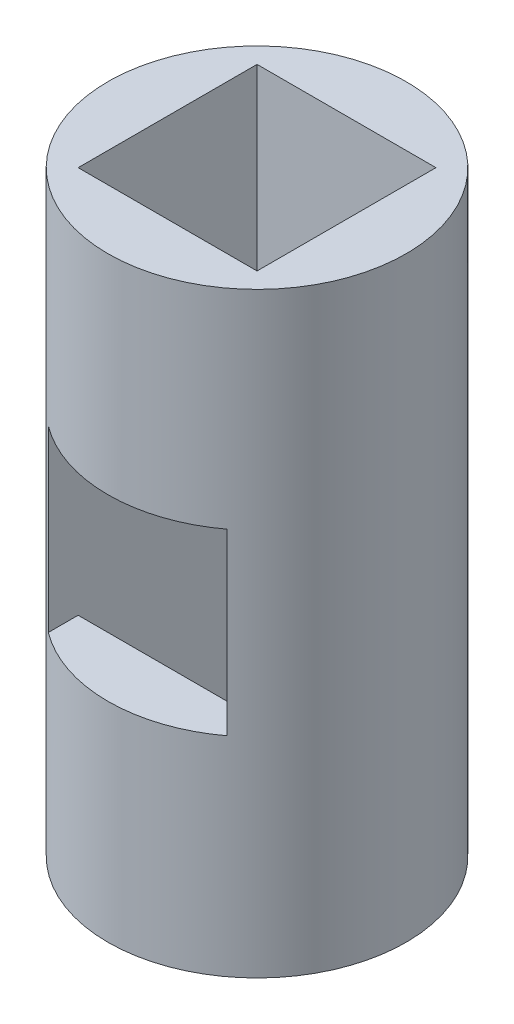
SolidWorks part; units mm, degrees
ref_plane "Front Plane" through (0, 0, 0) normal (0, 0, 1) x (1, 0, 0)
ref_plane "Top Plane" through (0, 0, 0) normal (0, 1, 0) x (1, 0, 0)
ref_plane "Right Plane" through (0, 0, 0) normal (1, 0, 0) x (0, 0, -1)
sketch "Sketch1" plane through (0, 0, 0) normal (0, 1, 0) x (1, 0, 0)
  circle A0 centre (0, 0) radius 25
  dimension "D1" = 50
extrude "Boss-Extrude1" add sketch "Sketch1" along normal blind 100
sketch3d "3DSketch4"
  line L1 (-15, 0, -15) -> (15, 0, -15)
  line L2 (-15, 0, -15) -> (-15, 0, 15)
  line L3 (-15, 0, 15) -> (15, 0, 15)
  line L4 (15, 0, -15) -> (15, 0, 15)
  line L5 (-15, 0, -15) -> (15, 0, 15) construction
  line L6 (-15, 0, 15) -> (15, 0, -15) construction
  point P0 (0, 0, 0)
  dimension "D1" = 30
  dimension "D2" = 30
extrude "Cut-Extrude1" cut sketch "3DSketch4" along a picked direction on the side of the normal up to next (100 mm away)
sketch "Sketch3" plane through (0, 0, -15) normal (0, 0, 1) x (1, 0, 0)
  line L0 (0, 0) -> (0, 100) construction
  line L1 (-15, 100) -> (15, 100) construction
  line L3 (-15, 65) -> (15, 65)
  line L4 (-15, 65) -> (-15, 35)
  line L5 (-15, 35) -> (15, 35)
  line L6 (15, 65) -> (15, 35)
  line L7 (-15, 65) -> (15, 35) construction
  line L8 (-15, 35) -> (15, 65) construction
  point P5 (0, 50)
  dimension "D1" = 30
  dimension "D2" = 30
extrude "Cut-Extrude2" cut sketch "Sketch3" against normal up to next
sketch "Sketch4" plane through (0, 0, 15) normal (0, 0, -1) x (-1, 0, 0)
  line L1 (-15, 65) -> (15, 65)
  line L2 (-15, 65) -> (-15, 35)
  line L3 (-15, 35) -> (15, 35)
  line L4 (15, 65) -> (15, 35)
extrude "Cut-Extrude3" cut sketch "Sketch4" against normal up to next
